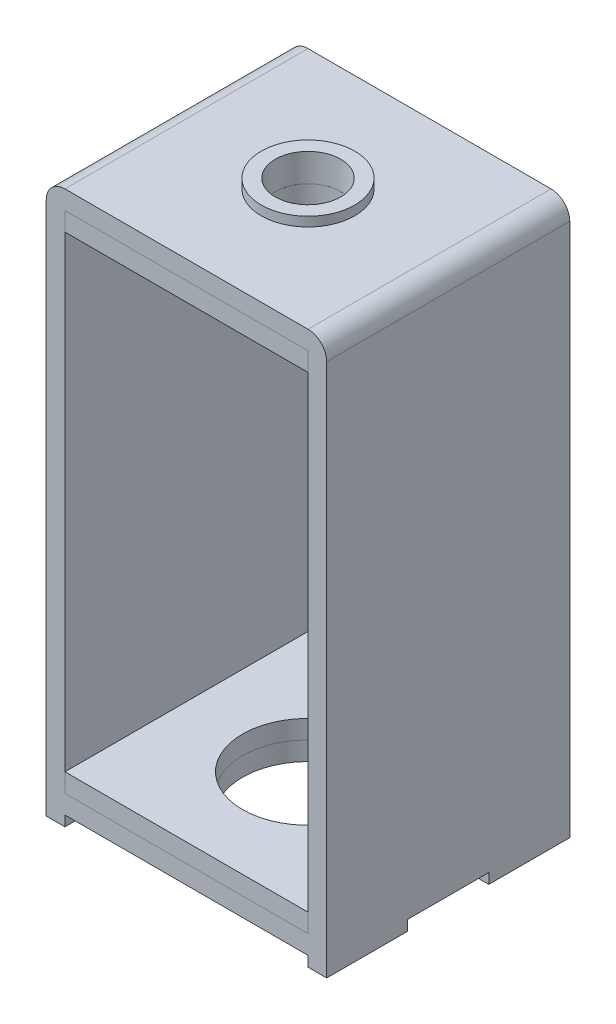
SolidWorks part; units mm, degrees
ref_plane "Front Plane" through (0, 0, 0) normal (0, 0, 1) x (1, 0, 0)
ref_plane "Top Plane" through (0, 0, 0) normal (0, 1, 0) x (1, 0, 0)
ref_plane "Right Plane" through (0, 0, 0) normal (1, 0, 0) x (0, 0, -1)
sketch "Sketch1" plane through (0, 0, 0) normal (0, 1, 0) x (1, 0, 0)
  line L1 (-5.8976, 6.5317) -> (9.1024, 6.5317)
  line L2 (-5.8976, 6.5317) -> (-5.8976, -6.4683)
  line L3 (-5.8976, -6.4683) -> (9.1024, -6.4683)
  line L4 (9.1024, 6.5317) -> (9.1024, -6.4683)
  dimension "D1" = 13
  dimension "D2" = 15
extrude "Boss-Extrude1" add sketch "Sketch1" along normal blind 1
sketch "Sketch2" plane through (0, 1, 0) normal (0, 1, 0) x (1, 0, 0)
  line L0 (-5.8976, -6.4683) -> (9.1024, -6.4683) construction
  line L1 (-5.8976, 6.5317) -> (-4.8976, 6.5317)
  line L2 (-5.8976, 6.5317) -> (-5.8976, -6.4683)
  line L3 (-5.8976, -6.4683) -> (-4.8976, -6.4683)
  line L4 (-4.8976, 6.5317) -> (-4.8976, -6.4683)
  line L6 (9.1024, 6.5317) -> (8.1024, 6.5317)
  line L7 (9.1024, 6.5317) -> (9.1024, -6.4683)
  line L8 (9.1024, -6.4683) -> (8.1024, -6.4683)
  line L9 (8.1024, 6.5317) -> (8.1024, -6.4683)
  dimension "D1" = 1
  dimension "D2" = 1
extrude "Boss-Extrude2" add sketch "Sketch2" along normal blind 27
sketch "Sketch3" plane through (0, 28, 0) normal (0, 1, 0) x (1, 0, 0)
  line L1 (-5.8976, 6.5317) -> (9.1024, 6.5317)
  line L2 (-5.8976, 6.5317) -> (-5.8976, -6.4683)
  line L3 (-5.8976, -6.4683) -> (9.1024, -6.4683)
  line L4 (9.1024, 6.5317) -> (9.1024, -6.4683)
extrude "Boss-Extrude3" add sketch "Sketch3" along normal blind 1
fillet "Fillet1" radius 1 1 edges at (-5.8976, 29, -0.0317)
fillet "Fillet2" radius 1 1 edges at (9.1024, 29, -0.0317)
sketch "Sketch4" plane through (0, 0, 0) normal (0, -1, 0) x (1, 0, 0)
  line L0 (-4.8976, 6.4683) -> (-5.8976, 6.4683)
  line L1 (9.1024, 6.4683) -> (8.1024, 6.4683)
  line L2 (9.1024, 6.4683) -> (9.1024, 2.1383)
  line L3 (9.1024, 2.1383) -> (8.1024, 2.1383)
  line L4 (8.1024, 6.4683) -> (8.1024, 2.1383)
  line L5 (-4.8976, 6.4683) -> (-4.8976, 2.1383)
  line L6 (-4.8976, 2.1383) -> (-5.8976, 2.1383)
  line L7 (-5.8976, 6.4683) -> (-5.8976, 2.1383)
  line L8 (-4.8976, -2.2017) -> (-5.8976, -2.2017)
  line L9 (9.1024, -2.2017) -> (8.1024, -2.2017)
  line L10 (9.1024, -2.2017) -> (9.1024, -6.5317)
  line L11 (9.1024, -6.5317) -> (8.1024, -6.5317)
  line L12 (8.1024, -2.2017) -> (8.1024, -6.5317)
  line L13 (-4.8976, -2.2017) -> (-4.8976, -6.5317)
  line L14 (-4.8976, -6.5317) -> (-5.8976, -6.5317)
  line L15 (-5.8976, -2.2017) -> (-5.8976, -6.5317)
  dimension "D1" = 1
  dimension "D2" = 4.33
  dimension "D3" = 1
  dimension "D4" = 4.33
  dimension "D5" = 1
  dimension "D6" = 4.33
  dimension "D7" = 1
  dimension "D8" = 4.33
extrude "Boss-Extrude4" add sketch "Sketch4" along normal blind 0.55
sketch "Sketch5" plane through (0, 1, 0) normal (0, 1, 0) x (1, 0, 0)
  line L1 (-4.8976, 6.5317) -> (8.1024, 6.5317)
  line L2 (-4.8976, 6.5317) -> (-4.8976, -6.4683)
  line L3 (-4.8976, -6.4683) -> (8.1024, -6.4683)
  line L4 (8.1024, 6.5317) -> (8.1024, -6.4683)
extrude "Boss-Extrude5" add sketch "Sketch5" along normal blind 1 separate body
sketch "Sketch7" plane through (0, 28, 0) normal (0, -1, 0) x (1, 0, 0)
  line L1 (8.1024, -6.5317) -> (-4.8976, -6.5317)
  line L2 (8.1024, -6.5317) -> (8.1024, 6.4683)
  line L3 (8.1024, 6.4683) -> (-4.8976, 6.4683)
  line L4 (-4.8976, -6.5317) -> (-4.8976, 6.4683)
extrude "Boss-Extrude6" add sketch "Sketch7" along normal blind 1 separate body
sketch "Sketch8" plane through (0, 2, 0) normal (0, 1, 0) x (1, 0, 0)
  line L0 (-4.8976, 6.5317) -> (8.1024, -6.4683) construction
  circle A0 centre (1.6024, 0.0317) radius 3.5
  dimension "D1" = 7
extrude "Cut-Extrude1" cut sketch "Sketch8" against normal through all
sketch "Sketch9" plane through (0, 27, 0) normal (0, -1, 0) x (1, 0, 0)
  line L0 (-4.8976, 6.4683) -> (8.1024, -6.5317) construction
  circle A0 centre (1.6024, -0.0317) radius 1.75
  dimension "D1" = 3.5
extrude "Cut-Extrude2" cut sketch "Sketch9" against normal through all
sketch "Sketch10" plane through (0, 29, 0) normal (0, 1, 0) x (1, 0, 0)
  circle A0 centre (1.6024, 0.0317) radius 1.75
  circle A1 centre (1.6024, 0.0317) radius 2.5
  dimension "D1" = 0.75
extrude "Boss-Extrude7" add sketch "Sketch10" along normal blind 0.5
